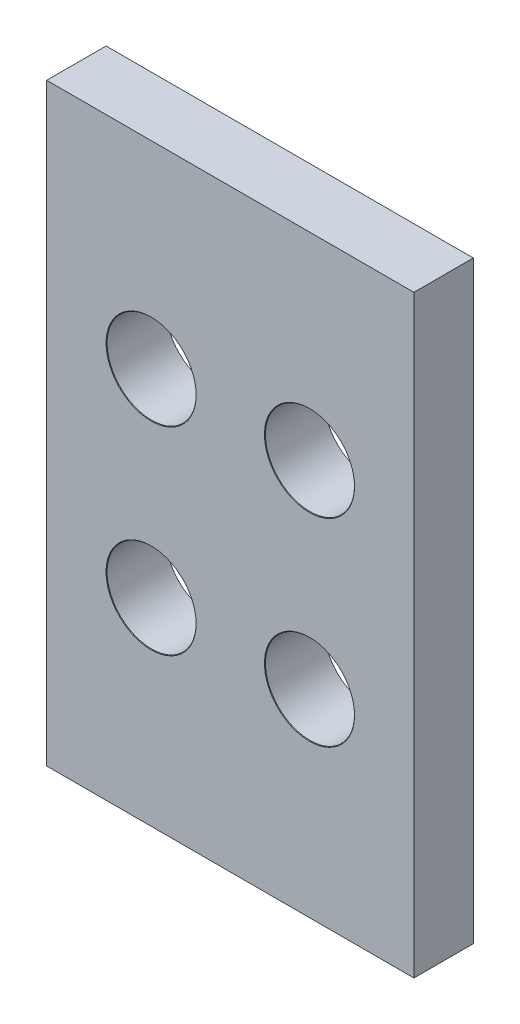
SolidWorks part; units mm, degrees
ref_plane "정면" through (0, 0, 0) normal (0, 0, 1) x (1, 0, 0)
ref_plane "윗면" through (0, 0, 0) normal (0, 1, 0) x (1, 0, 0)
ref_plane "우측면" through (0, 0, 0) normal (1, 0, 0) x (0, 0, -1)
sketch "스케치1" plane through (0, 0, 0) normal (0, 0, 1) x (1, 0, 0)
  line L0 (-24.4748, 0) -> (26.5222, 0) construction
  line L1 (0, 23.8855) -> (0, -25.9328) construction
  line L3 (9.275, -15) -> (-9.275, -15)
  line L4 (9.275, -15) -> (9.275, 15)
  line L5 (9.275, 15) -> (-9.275, 15)
  line L6 (-9.275, -15) -> (-9.275, 15)
  dimension "D1" = 18.55
  dimension "D2" = 9.275
  dimension "D3" = 30
  dimension "D4" = 15
extrude "보스-돌출1" add sketch "스케치1" along normal mid plane 3
sketch "스케치2" plane through (0, 0, 1.5) normal (0, 0, 1) x (1, 0, 0)
  line L0 (-15.543, 0) -> (17.9459, 0) construction
  line L1 (0, 21.3881) -> (0, -21.108) construction
  line L8 (-9.275, 15) -> (-9.275, -15) construction
  circle A2 centre (-4, 5.005) radius 2.275
  point P5 (4, 5.005)
  point P7 (-4, 5.005)
  point P8 (4, -5.005)
  point P9 (-4, -5.005)
  dimension "D1" = 5.275
  dimension "D4" = 2.73
  dimension "D2" = 4.55
  dimension "D3" = 8
hole_wizard "M4 여유 구멍1" positions "스케치2" profile "스케치3" hole size "M4" standard "KS" end condition up to next
sketch "스케치3" plane through (-4, -5.005, 1.5) normal (1, 0, 0) x (0, -1, 0)
  line L0 (0, 0) -> (0, 3)
  line L1 (0, 3) -> (2.25, 3)
  line L2 (2.25, 3) -> (2.25, 0.0241)
  line L3 (2.25, 0.0241) -> (2.275, 0)
  line L5 (2.275, 0) -> (0, 0)
  line L6 (-2.25, 0.0241) -> (-2.275, 0) construction
  line L11 (0, -6.35) -> (0, 107.95) construction
  dimension "관통 구멍 지름" = 4.5
  dimension "관통 구멍 깊이" = 3
  dimension "표면 카운터싱크 지름" = 4.55
  dimension "표면 카운터싱크 각도" = 92
